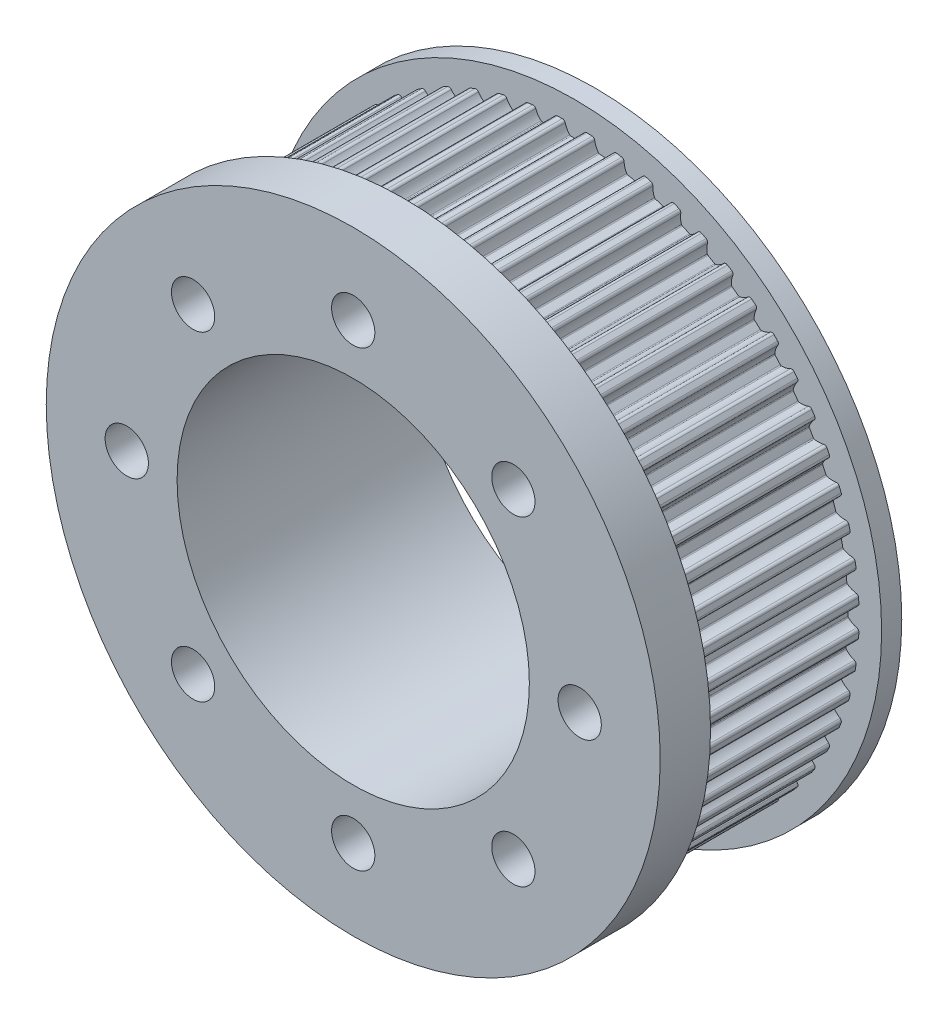
SolidWorks part; units mm, degrees
material "6061-T6 (SS)"
ref_plane "前基準面" through (0, 0, 0) normal (0, 0, 1) x (1, 0, 0)
ref_plane "上基準面" through (0, 0, 0) normal (0, 1, 0) x (1, 0, 0)
ref_plane "右基準面" through (0, 0, 0) normal (1, 0, 0) x (0, 0, -1)
sketch "草圖1" plane through (0, 0, 0) normal (0, 0, 1) x (1, 0, 0)
  circle A0 centre (0, 0) radius 28.265
  dimension "D1" = 56.53
extrude "填料-伸長1" add sketch "草圖1" along normal mid plane 17
sketch "草圖2" plane through (0, 0, 8.5) normal (0, 0, 1) x (1, 0, 0)
  line L0 (0, 0) -> (0, 28.265) construction
  line L1 (0, 28.265) -> (0, 28.519) construction
  line L2 (-0.975, 28.519) -> (0.975, 28.519) construction
  circle A0 centre (0, 0) radius 28.265 construction
  arc A1 (-0.3831, 27.1523) -> (0.3831, 27.1523) centre (0, 0) cw
  arc A2 (-0.3831, 27.1523) -> (-0.497, 27.2023) centre (-0.3852, 27.3023) cw
  arc A3 (-0.497, 27.2023) -> (-0.9381, 28.0284) centre (0.975, 28.519) cw
  arc A4 (-1.2214, 28.2386) -> (-0.9381, 28.0284) centre (-1.2093, 27.9589) cw
  arc A5 (0.3831, 27.1523) -> (0.497, 27.2023) centre (0.3852, 27.3023) ccw
  arc A6 (0.497, 27.2023) -> (0.9381, 28.0284) centre (-0.975, 28.519) ccw
  arc A7 (1.2214, 28.2386) -> (0.9381, 28.0284) centre (1.2093, 27.9589) ccw
  arc A8 (-1.2214, 28.2386) -> (1.2214, 28.2386) centre (0, 0) cw
  dimension "D1" = 0.15
  dimension "D2" = 1.975
  dimension "D3" = 0.28
  dimension "D4" = 1.11
  dimension "D5" = 0.254
  dimension "D6" = 1.95
extrude "除料-伸長1" cut sketch "草圖2" against normal through all and the other way through all
pattern_circular "環狀複製排列1" count 60 over 360 about axis through (0, 0, 0) along (0, 0, 1) of "除料-伸長1"
sketch "草圖3" plane through (0, 0, 8.5) normal (0, 0, 1) x (1, 0, 0)
  circle A0 centre (0, 0) radius 30.5
  dimension "D1" = 61
extrude "填料-伸長2" add sketch "草圖3" along normal blind 5
sketch "草圖9" plane through (0, 0, -8.5) normal (0, 0, -1) x (-1, 0, 0)
  circle A0 centre (0, 0) radius 30.5
  circle A1 centre (0, 0) radius 30.5 construction
extrude "填料-伸長3" add sketch "草圖9" along normal blind 2
sketch "草圖4" plane through (0, 0, 13.5) normal (0, 0, 1) x (1, 0, 0)
  circle A0 centre (0, 0) radius 17.5
  dimension "D1" = 35
extrude "除料-伸長2" cut sketch "草圖4" against normal through all
hole_wizard "M4 餘隙孔2" positions "草圖7" profile "草圖8" hole size "M4" standard "Ansi Metric" end condition through all
sketch "草圖7" plane through (0, 0, 13.5) normal (0, 0, 1) x (1, 0, 0)
  line L0 (0, 22.5) -> (0, -22.5) construction
  point P1 (0, 22.5)
  dimension "D1" = 45
sketch "草圖8" plane through (0, 22.5, 13.5) normal (1, 0, 0) x (0, -1, 0)
  line L0 (0, 0) -> (0, 24)
  line L1 (0, 24) -> (2.15, 24)
  line L2 (2.15, 24) -> (2.15, 0)
  line L5 (2.15, 0) -> (0, 0)
  line L11 (0, -6.35) -> (0, 107.95) construction
  dimension "貫穿孔直徑" = 4.3
  dimension "貫穿孔深度" = 24
pattern_circular "環狀複製排列2" count 8 over 360 about axis through (0, 0, 0) along (0, 0, 1) of "M4 餘隙孔2"
